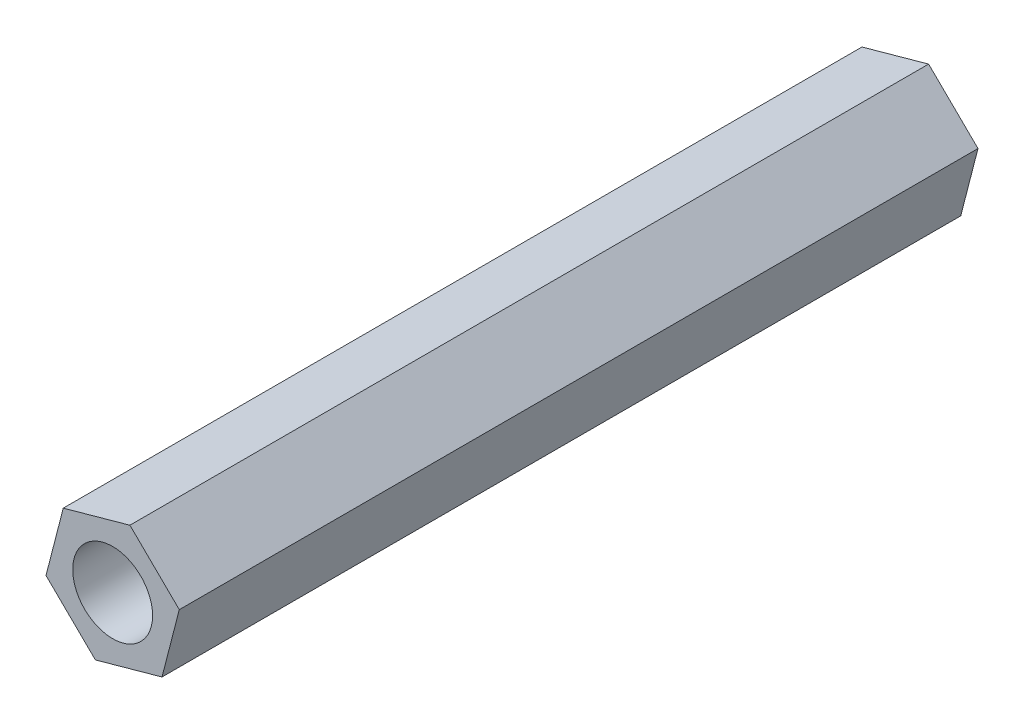
SolidWorks part; units mm, degrees
ref_plane "前视基准面" through (0, 0, 0) normal (0, 0, 1) x (1, 0, 0)
ref_plane "上视基准面" through (0, 0, 0) normal (0, 1, 0) x (1, 0, 0)
ref_plane "右视基准面" through (0, 0, 0) normal (1, 0, 0) x (0, 0, -1)
sketch "草图1" plane through (0, 0, 0) normal (0, 0, 1) x (1, 0, 0)
  line L1 (1.2361, -1.2132) -> (1.6688, 0.4639)
  line L2 (1.6688, 0.4639) -> (0.4326, 1.6771)
  line L3 (0.4326, 1.6771) -> (-1.2361, 1.2132)
  line L4 (-1.2361, 1.2132) -> (-1.6688, -0.4639)
  line L5 (-1.6688, -0.4639) -> (-0.4326, -1.6771)
  line L6 (-0.4326, -1.6771) -> (1.2361, -1.2132)
  circle A0 centre (0, 0) radius 1.5 construction
  dimension "D1" = 3
extrude "凸台-拉伸1" add sketch "草图1" along normal blind 20
sketch "草图2" plane through (0, 0, 20) normal (0, 0, 1) x (1, 0, 0)
  circle A0 centre (0, 0) radius 1
  dimension "D1" = 2
extrude "切除-拉伸1" cut sketch "草图2" against normal blind 20
